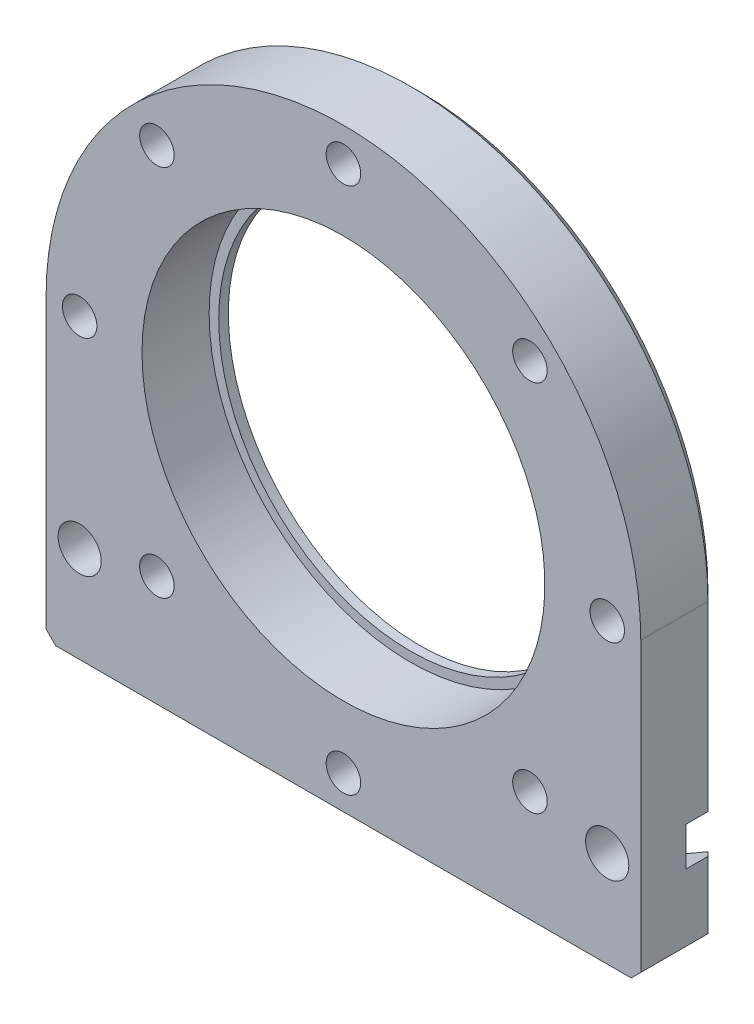
SolidWorks part; units mm, degrees
material "ABS"
ref_plane "正面" through (0, 0, 0) normal (0, 0, 1) x (1, 0, 0)
ref_plane "平面" through (0, 0, 0) normal (0, 1, 0) x (1, 0, 0)
ref_plane "右側面" through (0, 0, 0) normal (1, 0, 0) x (0, 0, -1)
sketch "ｽｹｯﾁ1" plane through (0, 0, 0) normal (0, 0, 1) x (1, 0, 0)
  line L0 (0, 0) -> (0, -31) construction
  line L1 (31, -31) -> (-31, -31)
  line L2 (-31, 0) -> (-31, -31)
  line L3 (31, 0) -> (31, -31)
  circle A0 centre (0, 0) radius 31 construction
  arc A1 (-31, 0) -> (31, 0) centre (0, 0) cw
  point P8 (0, -31)
  dimension "D1" = 62
extrude "ﾎﾞｽ - 押し出し1" add sketch "ｽｹｯﾁ1" along normal blind 8
sketch "ｽｹｯﾁ2" plane through (0, 0, 8) normal (0, 0, 1) x (1, 0, 0)
  circle A0 centre (0, 0) radius 20
  dimension "D1" = 40
extrude "ｶｯﾄ - 押し出し1" cut sketch "ｽｹｯﾁ2" against normal through all
hole_wizard "M3 すきま穴1" positions "ｽｹｯﾁ3" profile "ｽｹｯﾁ4" hole size "M3" standard "JIS" end condition through all
sketch "ｽｹｯﾁ3" plane through (0, 0, 8) normal (0, 0, 1) x (1, 0, 0)
  point P0 (0, 27.5)
  dimension "D1" = 27.5
sketch "ｽｹｯﾁ4" plane through (0, 27.5, 8) normal (1, 0, 0) x (0, -1, 0)
  line L0 (0, 0) -> (0, 8)
  line L1 (0, 8) -> (1.8, 8)
  line L2 (1.8, 8) -> (1.8, 0)
  line L5 (1.8, 0) -> (0, 0)
  line L11 (0, -6.35) -> (0, 107.95) construction
  dimension "通し穴の直径" = 3.6
  dimension "通し穴の深さ" = 8
pattern_circular "円形ﾊﾟﾀｰﾝ1" count 8 over 360 about axis through (0, 0, 0) along (0, 0, 1) of "M3 すきま穴1"
chamfer "面取り1" distance 1 angle 45 6 edges at (31, -31, 4) (-31, -31, 4) (31, -15.5, 0) (0, -31, 0) (-31, -15.5, 0) (0, 31, 0)
hole_wizard "M4 すきま穴1" positions "ｽｹｯﾁ5" profile "ｽｹｯﾁ6" hole size "M4" standard "JIS" end condition through all
sketch "ｽｹｯﾁ5" plane through (0, 0, 8) normal (0, 0, 1) x (1, 0, 0)
  line L0 (-27.5, -21) -> (27.5, -21) construction
  line L2 (-30, -31) -> (30, -31) construction
  line L3 (0, 0) -> (0, -21) construction
  point P0 (-27.5, -21)
  point P2 (27.5, -21)
  dimension "D2" = 55
  dimension "D1" = 10
sketch "ｽｹｯﾁ6" plane through (-27.5, -21, 8) normal (1, 0, 0) x (0, -1, 0)
  line L0 (0, 0) -> (0, 8)
  line L1 (0, 8) -> (2.25, 8)
  line L2 (2.25, 8) -> (2.25, 0)
  line L5 (2.25, 0) -> (0, 0)
  line L11 (0, -6.35) -> (0, 107.95) construction
  dimension "通し穴の直径" = 4.5
  dimension "通し穴の深さ" = 8
sketch "ｽｹｯﾁ7" plane through (0, 0, 0) normal (0, 0, 1) x (1, 0, 0)
  line L1 (-27.5, -25.0415) -> (-24, -23.0207)
  line L2 (-24, -23.0207) -> (-24, -18.9793)
  line L3 (-24, -18.9793) -> (-27.5, -16.9585)
  line L4 (-27.5, -16.9585) -> (-31, -18.9793)
  line L5 (-31, -18.9793) -> (-31, -23.0207)
  line L6 (-31, -23.0207) -> (-27.5, -25.0415)
  line L7 (31, -18.9793) -> (27.5, -16.9585)
  line L8 (27.5, -16.9585) -> (24, -18.9793)
  line L9 (24, -18.9793) -> (24, -23.0207)
  line L10 (24, -23.0207) -> (27.5, -25.0415)
  line L11 (27.5, -25.0415) -> (31, -23.0207)
  line L12 (31, -23.0207) -> (31, -18.9793)
  circle A0 centre (-27.5, -21) radius 3.5 construction
  circle A1 centre (27.5, -21) radius 3.5 construction
  dimension "D1" = 7
  dimension "D2" = 7
extrude "ｶｯﾄ - 押し出し2" cut sketch "ｽｹｯﾁ7" along normal blind 3.3
sketch "ｽｹｯﾁ8" plane through (0, 0, 8) normal (0, 0, -1) x (-1, 0, 0)
  circle A0 centre (0, 0) radius 21
  dimension "D1" = 42
extrude "ｶｯﾄ - 押し出し3" cut sketch "ｽｹｯﾁ8" along normal blind 7
